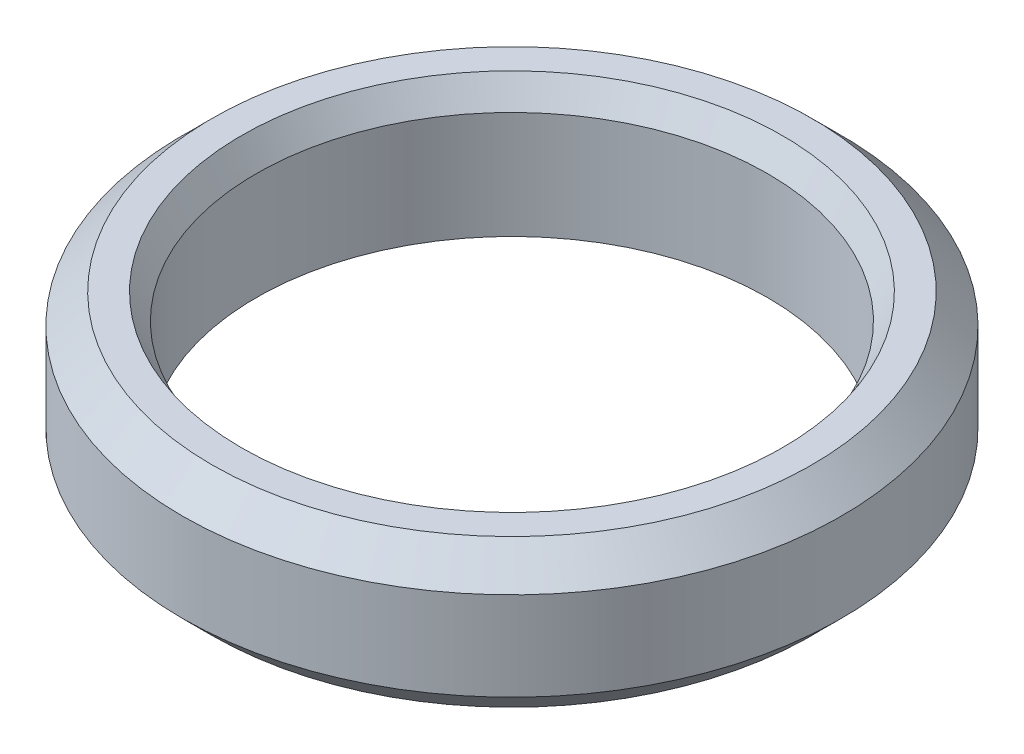
SolidWorks part; units mm, degrees
ref_plane "Front Plane" through (0, 0, 0) normal (0, 0, 1) x (1, 0, 0)
ref_plane "Top Plane" through (0, 0, 0) normal (0, 1, 0) x (1, 0, 0)
ref_plane "Right Plane" through (0, 0, 0) normal (1, 0, 0) x (0, 0, -1)
sketch "Sketch1" plane through (0, 0, 0) normal (0, 1, 0) x (1, 0, 0)
  circle A0 centre (0, 0) radius 8.65
  circle A1 centre (0, 0) radius 11.15
  dimension "D1" = 17.3
  dimension "D2" = 2.5
extrude "Boss-Extrude1" add sketch "Sketch1" along normal blind 5
chamfer "Chamfer1" distance 1 angle 45 2 edges at (0, 0, 11.15) (0, 5, 11.15)
chamfer "Chamfer2" distance 0.5 angle 60 2 edges at (0, 0, 8.65) (0, 5, 8.65)
